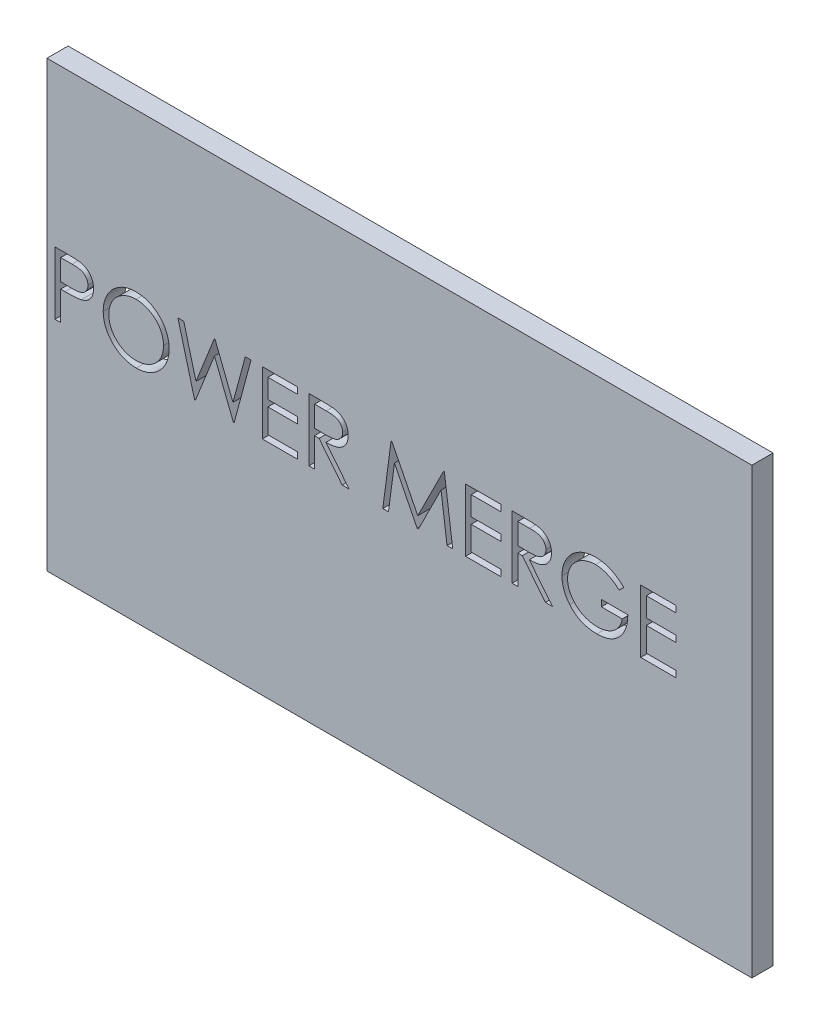
SolidWorks part; units mm, degrees
ref_plane "Front Plane" through (0, 0, 0) normal (0, 0, 1) x (1, 0, 0)
ref_plane "Top Plane" through (0, 0, 0) normal (0, 1, 0) x (1, 0, 0)
ref_plane "Right Plane" through (0, 0, 0) normal (1, 0, 0) x (0, 0, -1)
sketch "Sketch1" plane through (0, 0, 0) normal (0, 0, 1) x (1, 0, 0)
  line L1 (-50, 31.5) -> (50, 31.5)
  line L2 (-50, 31.5) -> (-50, -31.5)
  line L3 (-50, -31.5) -> (50, -31.5)
  line L4 (50, 31.5) -> (50, -31.5)
  line L5 (-50, 31.5) -> (50, -31.5) construction
  line L6 (-50, -31.5) -> (50, 31.5) construction
  point P0 (0, 0)
  dimension "D1" = 100
  dimension "D2" = 63
extrude "Boss-Extrude1" add sketch "Sketch1" along normal blind 3
sketch "Sketch2" plane through (0, 0, 3) normal (0, 0, 1) x (1, 0, 0)
  line L0 (-50, 0) -> (50, 0) construction
  line L1 (-50, 31.5) -> (-50, -31.5) construction
  line L2 (50, -31.5) -> (50, 31.5) construction
  text T0 "POWER MERGE" font "Century Gothic" height 8.89
extrude "Cut-Extrude1" cut sketch "Sketch2" against normal through all both and the other way through all
